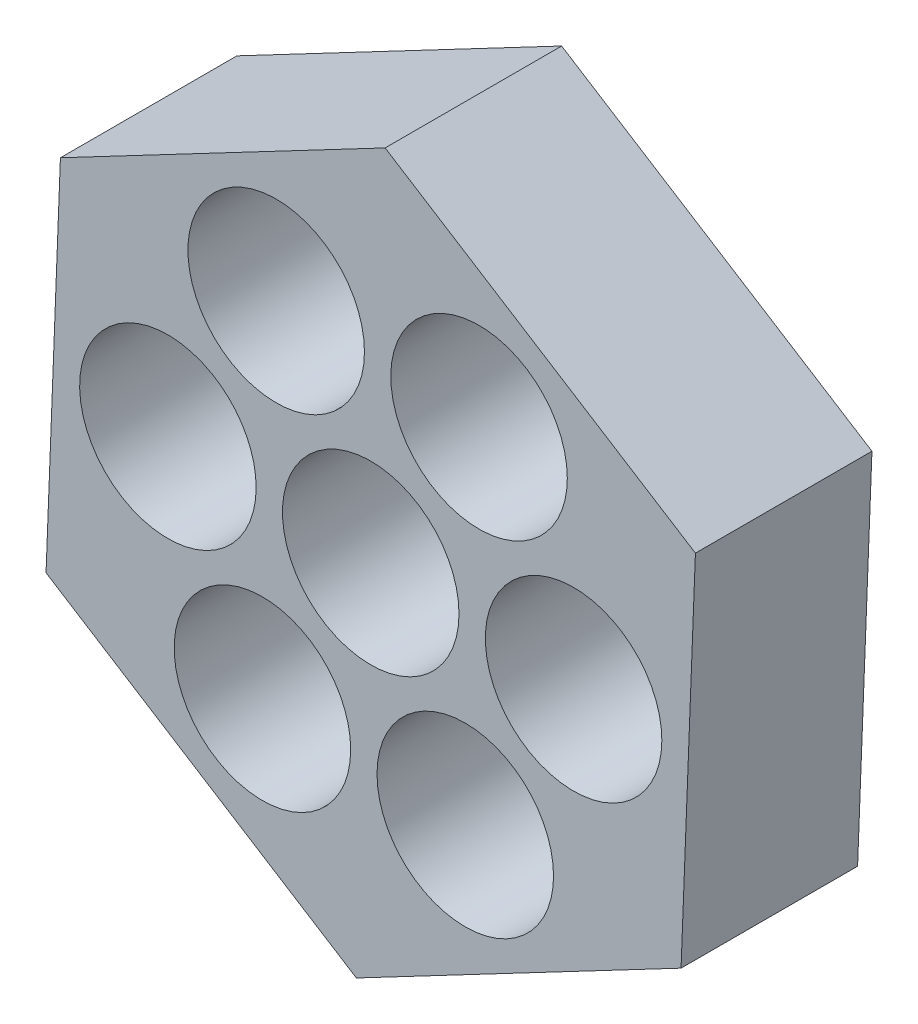
SolidWorks part; units mm, degrees
ref_plane "Front Plane" through (0, 0, 0) normal (0, 0, 1) x (1, 0, 0)
ref_plane "Top Plane" through (0, 0, 0) normal (0, 1, 0) x (1, 0, 0)
ref_plane "Right Plane" through (0, 0, 0) normal (1, 0, 0) x (0, 0, -1)
sketch "Sketch1" plane through (0, 0, 0) normal (0, 0, 1) x (1, 0, 0)
  line L0 (-8.7895, 5.5447) -> (-9.1966, -4.8396)
  line L1 (8.7895, -5.5447) -> (9.1966, 4.8396)
  line L2 (9.1966, 4.8396) -> (0.4071, 10.3843)
  line L3 (0.4071, 10.3843) -> (-8.7895, 5.5447)
  line L4 (-9.1966, -4.8396) -> (-0.4071, -10.3843)
  line L5 (-0.4071, -10.3843) -> (8.7895, -5.5447)
  circle A0 centre (0, 0) radius 9 construction
  circle A1 centre (0, 0) radius 2.5
  dimension "D1" = 18
  dimension "D2" = 5
extrude "Boss-Extrude1" add sketch "Sketch1" along normal blind 5
sketch "Sketch2" plane through (0, 0, 5) normal (0, 0, 1) x (1, 0, 0)
  line L0 (-4.1912, 7.9645) -> (-1.1642, 2.2124) construction
  line L1 (0.4071, 10.3843) -> (-8.7895, 5.5447) construction
  circle A0 centre (0, 0) radius 2.5 construction
  circle A1 centre (-2.6777, 5.0884) radius 2.5
  dimension "D1" = 5
extrude "Cut-Extrude1" cut sketch "Sketch2" against normal blind 9 contours A1
pattern_circular "CirPattern1" count 6 over 360 about axis through (0, 0, 0) along (0, 0, 1) of "Cut-Extrude1"
